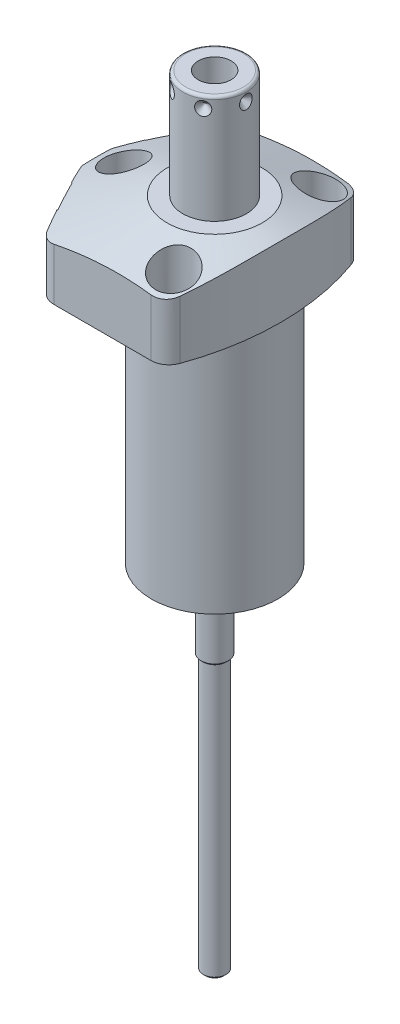
SolidWorks part; units mm, degrees
material "Alloy Steel"
ref_plane "Front Plane" through (0, 0, 0) normal (0, 0, 1) x (1, 0, 0)
ref_plane "Top Plane" through (0, 0, 0) normal (0, 1, 0) x (1, 0, 0)
ref_plane "Right Plane" through (0, 0, 0) normal (1, 0, 0) x (0, 0, -1)
ref_plane "Plane1" through (0, 0, 0) normal (0, 0, 1) x (0, -1, 0)
sketch "Sketch1" plane through (0, 0, 0) normal (0, 0, 1) x (0, -1, 0)
  line L0 (0, 44.45) -> (-26.9748, 44.45)
  line L1 (-26.9748, 44.45) -> (-26.9748, 0)
  line L2 (-26.9748, 0) -> (84.1502, 0)
  line L3 (84.1502, 0) -> (84.1502, 22.098)
  line L4 (84.1502, 22.098) -> (0, 22.098)
  line L5 (0, 22.098) -> (0, 44.45)
  line L6 (-32.531, 0) -> (89.7065, 0) construction
  dimension "D1" = 111.125
  dimension "D2" = 26.9748
  dimension "D3" = 88.9
  dimension "D4" = 44.196
revolve "Revolve1" add sketch "Sketch1" angle 360 about L6
ref_plane "Plane2" through (0, 0, 0) normal (0, -1, 0) x (0, 0, -1)
sketch "Sketch2" plane through (0, 0, 0) normal (0, -1, 0) x (0, 0, -1)
  line L0 (34.1122, -28.4984) -> (34.1122, 28.4984)
  line L2 (-34.1122, 28.4984) -> (-34.1122, -28.4984)
  line L3 (0, -32.1458) -> (0, 48.0974) construction
  arc A0 (34.1122, -28.4984) -> (34.1122, 28.4984) centre (0, 0) ccw
  circle A1 centre (0, 0) radius 44.45
  arc A2 (-34.1122, 28.4984) -> (-34.1122, -28.4984) centre (0, 0) ccw
  point P4 (0, 0)
  dimension "D1" = 68.2244
  dimension "D2" = 0
extrude "Cut-Extrude1" cut sketch "Sketch2" against normal up to next
ref_plane "Plane3" through (0, 0, 0) normal (0, -1, 0) x (-1, 0, 0)
sketch "Sketch3" plane through (0, 0, 0) normal (0, -1, 0) x (-1, 0, 0)
  line L0 (25.9049, 34.1122) -> (44.0427, 0)
  line L1 (44.0427, 0) -> (25.9049, -34.1122)
  line L2 (-39.4859, -20.995) -> (73.8214, 39.2515) construction
  line L3 (0, 0) -> (44.0427, 0) construction
  line L6 (-28.4984, -34.1122) -> (28.4984, -34.1122)
  line L7 (28.4984, 34.1122) -> (-28.4984, 34.1122)
  line L8 (25.9049, -34.1122) -> (28.4984, -34.1122)
  line L9 (28.4984, 34.1122) -> (25.9049, 34.1122)
  arc A2 (-28.4984, 34.1122) -> (-28.4984, -34.1122) centre (0, 0) ccw
  arc A3 (28.4984, -34.1122) -> (28.4984, 34.1122) centre (0, 0) ccw
  arc A5 (28.4984, -34.1122) -> (28.4984, 34.1122) centre (0, 0) ccw
  dimension "D1" = 28
  dimension "D2" = 38.8874
  dimension "D3" = 0
extrude "Cut-Extrude2" cut sketch "Sketch3" against normal up to next
ref_plane "Plane4" through (0, 0, 0) normal (0, -1, 0) x (-1, 0, 0)
sketch "S2D0002" plane through (0, 0, 0) normal (0, -1, 0) x (-1, 0, 0)
  line L0 (41.275, 85.425) -> (41.275, -85.425)
  arc A0 (41.275, 85.425) -> (41.275, -85.425) centre (65.8876, 0) ccw
  dimension "D3" = 88.9
  dimension "D1" = 65.8876
  dimension "D2" = 41.275
extrude "Cut-Extrude3" cut sketch "S2D0002" against normal blind 38.0873 flip side to cut
fillet "Fillet1" radius 6.35 2 edges at (16.2073, 13.4874, 34.1122) (16.2073, 13.4874, -34.1122)
fillet "Fillet2" radius 6.35 1 edges at (-25.9049, 13.4874, 34.1122)
fillet "Fillet3" radius 6.35 1 edges at (-25.9049, 13.4874, -34.1122)
ref_plane "Plane5" through (0, 0, 0) normal (0, 0, 1) x (1, 0, 0)
sketch "Sketch5" plane through (0, 0, 0) normal (0, 0, 1) x (1, 0, 0)
  line L0 (-16.637, 26.9748) -> (-47.625, 15.6961)
  line L1 (0, 7.6649) -> (0, 27.5963) construction
  line L3 (11.854, 26.9748) -> (-22.0895, 26.9748) construction
  line L4 (-16.637, 26.9748) -> (-47.625, 26.9748)
  line L5 (-47.625, 26.9748) -> (-47.625, 15.6961)
  dimension "D1" = 33.274
  dimension "D2" = 20
  dimension "D3" = 47.625
revolve "Cut-Revolve1" cut sketch "Sketch5" angle 360 about L1
ref_plane "Plane6" through (-34.1113, 10.287, -18.1373) normal (0, 1, 0) x (0.4695, 0, -0.8829)
sketch "Sketch6" plane through (-34.1113, 10.287, -18.1373) normal (0, 1, 0) x (0.4695, 0, -0.8829)
  line L0 (0, 0) -> (6.1849, 0)
  line L1 (6.1849, 0) -> (5.6423, -2.5527)
  line L2 (5.6423, -2.5527) -> (4.9784, -3.2166)
  line L3 (4.9784, -3.2166) -> (4.9784, -15.748)
  line L4 (4.9784, -15.748) -> (0, -15.748)
  line L5 (0, -15.748) -> (0, 0)
  line L6 (0, -16.5354) -> (0, 0.7874) construction
  dimension "D1" = 15.748
revolve "Cut-Revolve2" cut sketch "Sketch6" angle 360 about L6
ref_plane "Plane7" through (-34.1113, 10.287, 18.1373) normal (0, 1, 0) x (-0.4695, 0, -0.8829)
sketch "Sketch7" plane through (-34.1113, 10.287, 18.1373) normal (0, 1, 0) x (-0.4695, 0, -0.8829)
  line L0 (0, 0) -> (6.1849, 0)
  line L1 (6.1849, 0) -> (5.6423, -2.5527)
  line L2 (5.6423, -2.5527) -> (4.9784, -3.2166)
  line L3 (4.9784, -3.2166) -> (4.9784, -15.748)
  line L4 (4.9784, -15.748) -> (0, -15.748)
  line L5 (0, -15.748) -> (0, 0)
  line L6 (0, -16.5354) -> (0, 0.7874) construction
  dimension "D1" = 15.748
revolve "Cut-Revolve3" cut sketch "Sketch7" angle 360 about L6
ref_plane "Plane8" through (-13.4874, 2.667, -26.5938) normal (0, 0, 1) x (-1, 0, 0)
sketch "Sketch8" plane through (-13.4874, 2.667, -26.5938) normal (0, 0, 1) x (-1, 0, 0)
  line L0 (0, 0) -> (4.5466, 0)
  line L1 (4.5466, 0) -> (4.1066, -2.0701)
  line L2 (4.1066, -2.0701) -> (3.4544, -2.7223)
  line L3 (3.4544, -2.7223) -> (3.4544, -12.573)
  line L4 (3.4544, -12.573) -> (0, -12.573)
  line L5 (0, -12.573) -> (0, 0)
  line L6 (0, -13.2017) -> (0, 0.6287) construction
  dimension "D1" = 12.573
revolve "Cut-Revolve4" cut sketch "Sketch8" angle 360 about L6
ref_plane "Plane9" through (-13.4874, 2.667, 26.5938) normal (0, 0, 1) x (-1, 0, 0)
sketch "Sketch9" plane through (-13.4874, 2.667, 26.5938) normal (0, 0, 1) x (-1, 0, 0)
  line L0 (0, 0) -> (4.5466, 0)
  line L1 (4.5466, 0) -> (4.1066, -2.0701)
  line L2 (4.1066, -2.0701) -> (3.4544, -2.7223)
  line L3 (3.4544, -2.7223) -> (3.4544, -12.573)
  line L4 (3.4544, -12.573) -> (0, -12.573)
  line L5 (0, -12.573) -> (0, 0)
  line L6 (0, -13.2017) -> (0, 0.6287) construction
  dimension "D1" = 12.573
revolve "Cut-Revolve5" cut sketch "Sketch9" angle 360 about L6
sketch "Sketch17" plane through (-34.3355, 0, 18.2565) normal (-0.8829, 0, 0.4695) x (0.4695, 0, 0.8829)
  circle A0 centre (0, 10.287) radius 10.4775
  dimension "D1" = 20.955
extrude "Cut-Extrude4" cut sketch "Sketch17" against normal blind 0.254
sketch "Sketch18" plane through (0, 0, 0) normal (0, -1, 0) x (1, 0, 0)
  circle A0 centre (-13.4874, 26.5938) radius 5.5626
  dimension "D1" = 11.1252
extrude "Cut-Extrude5" cut sketch "Sketch18" against normal blind 2.667
mirror "Mirror1" about plane through (0, 0, 0) normal (0, 0, 1) of "Cut-Extrude5", "Cut-Extrude4"
ref_plane "Plane10" through (0, 0, 0) normal (1, 0, 0) x (0, 0, -1)
sketch "Sketch10" plane through (0, 0, 0) normal (1, 0, 0) x (0, 0, -1)
  line L0 (0, 26.9748) -> (-11.1125, 26.9748)
  line L1 (-11.1125, 26.9748) -> (-11.1125, 63.8302)
  line L2 (-10.0965, 64.8462) -> (0, 64.8462)
  line L3 (0, 64.8462) -> (0, 26.9748)
  line L4 (0, 14.3517) -> (0, 66.7398) construction
  line L5 (16.637, 26.9748) -> (-16.637, 26.9748) construction
  line L6 (-29.8978, 0) -> (29.8978, 0) construction
  arc A0 (-10.0965, 64.8462) -> (-11.1125, 63.8302) centre (-10.0965, 63.8302) ccw
  dimension "D2" = 1.016
  dimension "D1" = 64.8462
  dimension "D3" = 22.225
revolve "Revolve2" add sketch "Sketch10" angle 360 about L4
ref_plane "Plane11" through (5.7531, 64.8462, 0) normal (0, 0, 1) x (1, 0, 0)
sketch "S2D0001" plane through (5.7531, 64.8462, 0) normal (0, 0, 1) x (1, 0, 0)
  line L0 (0, 0) -> (0, -17.018)
  line L1 (0, -17.018) -> (-5.7531, -20.4748)
  line L2 (0, 0) -> (-5.7531, 0)
  line L3 (-5.7531, 0) -> (-5.7531, -20.4748)
  line L4 (-5.7531, -27.7363) -> (-5.7531, 1.0237) construction
  line L5 (4.3434, 0) -> (-15.8496, 0) construction
  dimension "D1" = 11.5062
  dimension "D2" = 17.018
  dimension "D3" = 59
revolve "Cut-Revolve6" cut sketch "S2D0001" angle 360 about L4
ref_plane "Plane13" through (-13.4874, 0, 26.5938) normal (1, 0, 0) x (0, 0, -1)
sketch "Sketch14" plane through (-13.4874, 0, 26.5938) normal (1, 0, 0) x (0, 0, -1)
  line L0 (5.461, 2.667) -> (5.461, 0.9398)
  line L1 (5.461, 0.9398) -> (5.3016, 0.9398)
  line L2 (2.667, 0.4318) -> (2.667, 0.127)
  line L3 (2.667, 0.127) -> (1.5875, 0.127)
  line L4 (1.5875, 0.127) -> (1.5875, 10.6172)
  line L5 (1.5875, 10.6172) -> (3.2512, 10.6172)
  line L6 (3.2512, 10.6172) -> (3.2512, 2.667)
  line L7 (3.2512, 2.667) -> (5.461, 2.667)
  line L8 (3.175, 0.9398) -> (3.8424, 0.9398)
  line L9 (0, -1.0109) -> (0, 11.1709) construction
  arc A0 (3.175, 0.9398) -> (2.667, 0.4318) centre (3.175, 0.4318) ccw
  arc A1 (3.8424, 0.9398) -> (5.3016, 0.9398) centre (4.572, 0.4318) ccw
  dimension "D1" = 2.54
  dimension "D2" = 7.9502
revolve "Revolve3" add sketch "Sketch14" angle 360 about L9
ref_plane "Plane14" through (-11.1125, 60.8838, 0) normal (0, 0, 1) x (0, 1, 0)
sketch "Sketch15" plane through (-11.1125, 60.8838, 0) normal (0, 0, 1) x (0, 1, 0)
  line L0 (0, 0) -> (2.413, 0)
  line L1 (2.413, 0) -> (0, -2.413)
  line L2 (0, 0) -> (0, -2.413)
  line L3 (0, -5.1094) -> (0, 0.1207) construction
  line L4 (2.9464, 0) -> (-33.909, 0) construction
  line L5 (3.9624, -21.209) -> (3.9624, -1.016) construction
  dimension "D1" = 3.9624
  dimension "D2" = 4.826
  dimension "D3" = 45
revolve "Cut-Revolve7" cut sketch "Sketch15" angle 360 about L3
pattern_circular "CirPattern1" count 6 over 360 about axis through (0, 14.3517, 0) along (0, -1, 0) of "Cut-Revolve7"
hole_wizard "Hole1" positions "Sketch20" profile "Sketch19" legacy end condition up to next
sketch "Sketch20" plane through (0, 26.9748, 0) normal (0, 1, 0) x (-1, 0, 0)
  line L0 (0, 0) -> (47.6205, 0) construction
  line L1 (0, 0) -> (0, 38.9977) construction
  point P0 (-11.1252, -25.4)
  point P10 (31.75, 0)
  point P14 (-11.1252, 25.4)
  dimension "D1" = 11.1252
  dimension "D2" = 25.4
  dimension "D3" = 31.75
sketch "Sketch19" plane through (11.1252, 26.9748, -25.4) normal (1, 0, 0) x (0, 0, 1)
  line L0 (0, 0) -> (0, 26.9748)
  line L1 (0, 26.9748) -> (4.3688, 26.9748)
  line L2 (4.3688, 26.9748) -> (4.3688, 16.6624)
  line L3 (4.3688, 16.6624) -> (6.9977, 16.6624)
  line L4 (6.9977, 16.6624) -> (6.9977, 0)
  line L5 (6.9977, 0) -> (0, 0)
  line L6 (0, 110) -> (0, -10) construction
  dimension "Diameter" = 8.7376
  dimension "Depth" = 26.9748
  dimension "C-Bore Diameter" = 13.9954
  dimension "C-Bore Depth" = 16.6624
mirror "Mirror2" about plane through (0, 0, 0) normal (0, 0, 1) of "Revolve3"
sketch "Sketch21" plane through (0, -84.1502, 0) normal (0, -1, 0) x (1, 0, 0)
  circle A0 centre (0, 0) radius 20.7772
  dimension "D1" = 41.5544
extrude "Extrude1" add sketch "Sketch21" along normal blind 1.016
sketch "Sketch22" plane through (0, -84.1502, 0) normal (0, -1, 0) x (1, 0, 0)
  circle A0 centre (0, 0) radius 20.7772 construction
  circle A1 centre (0, 0) radius 20.7772
  circle A2 centre (0, 0) radius 21.0312
  dimension "D1" = 42.0624
extrude "Cut-Extrude6" cut sketch "Sketch22" against normal blind 1.524
sketch "Sketch31" plane through (0, -85.1662, 0) normal (0, -1, 0) x (1, 0, 0)
  line L0 (0, 0) -> (0, 30.8242) construction
  line L1 (19.0433, 0) -> (-7.323, 0) construction
  line L2 (-1.1938, 8.6428) -> (-1.1938, 20.7429)
  line L3 (1.1938, 8.6428) -> (1.1938, 20.7429)
  line L4 (-1.1938, -8.6428) -> (-1.1938, -20.7429)
  line L5 (1.1938, -8.6428) -> (1.1938, -20.7429)
  arc A0 (-1.1938, 8.6428) -> (-1.1938, -8.6428) centre (0, 0) ccw
  circle A1 centre (0, 0) radius 20.7772 construction
  arc A2 (-1.1938, -20.7429) -> (1.1938, -20.7429) centre (0, 0) ccw
  arc A3 (1.1938, -8.6428) -> (1.1938, 8.6428) centre (0, 0) ccw
  arc A4 (1.1938, 20.7429) -> (-1.1938, 20.7429) centre (0, 0) ccw
  dimension "D2" = 17.4498
  dimension "D1" = 2.3876
extrude "Cut-Extrude7" cut sketch "Sketch31" against normal blind 1.524
sketch "Sketch32" plane through (0, 0, 0) normal (0, 0, 1) x (1, 0, 0)
  line L0 (0, 0) -> (0, -132.6962) construction
  line L1 (4.7625, -83.6422) -> (4.7625, -111.4806)
  line L2 (1.1938, -83.6422) -> (8.7249, -83.6422) construction
  line L3 (4.7625, -111.4806) -> (3.9624, -112.2807)
  line L4 (3.9624, -112.2807) -> (3.9624, -207.6196)
  line L5 (3.9624, -207.6196) -> (0, -207.6196)
  line L6 (0, -207.6196) -> (0, -83.6422)
  line L7 (0, -83.6422) -> (4.7625, -83.6422)
  line L8 (10.0965, 64.8462) -> (-10.0965, 64.8462) construction
  dimension "D1" = 9.525
  dimension "D2" = 7.9248
  dimension "D3" = 45
  dimension "D4" = 96.139
  dimension "D5" = 272.4658
revolve "Revolve4" add sketch "Sketch32" angle 360 about L0
chamfer "Chamfer1" distance 0.762 angle 45 3 edges at (0, -207.6196, 3.9624) (20.7772, -85.1662, 0) (-20.7772, -85.1662, 0)
